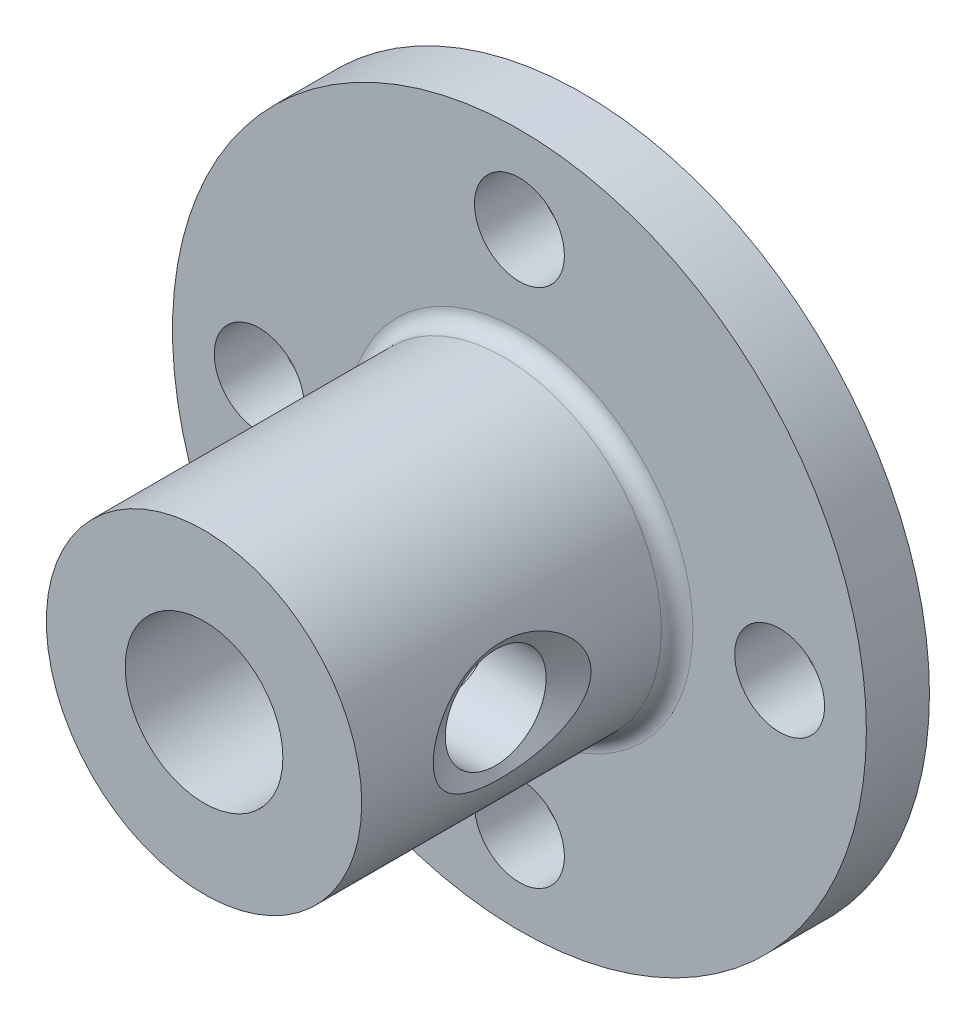
SolidWorks part; units mm, degrees
material "Cast Alloy Steel"
ref_plane "Front Plane" through (0, 0, 0) normal (0, 0, 1) x (1, 0, 0)
ref_plane "Top Plane" through (0, 0, 0) normal (0, 1, 0) x (1, 0, 0)
ref_plane "Right Plane" through (0, 0, 0) normal (1, 0, 0) x (0, 0, -1)
sketch "Sketch1" plane through (0, 0, 0) normal (0, 0, 1) x (1, 0, 0)
  circle A0 centre (0, 0) radius 2.5
  circle A1 centre (0, 0) radius 5
  circle A2 centre (0, 0) radius 11
sketch "Sketch3" plane through (0, 0, 0) normal (0, 0, 1) x (1, 0, 0)
  circle A0 centre (0, 0) radius 2.5
  circle A1 centre (0, 0) radius 5
  circle A2 centre (0, 0) radius 11
extrude "Boss-Extrude2" add sketch "Sketch1" along normal blind 12 contours A1 A0
extrude "Boss-Extrude3" add sketch "Sketch3" along normal blind 2 contours A2 A1
fillet "Fillet1" radius 0.5 1 edges at (5, 0, 2)
sketch "Sketch5" plane through (0, 0, 2) normal (0, 0, 1) x (1, 0, 0)
  line L0 (0, 0) -> (0, 11)
  line L1 (0, -6.6) -> (0, 6.6) construction
  line L2 (0, 11) -> (0, 5.5)
  line L3 (0, 5.5) -> (0, 8.25)
  line L4 (0, 0) -> (0, -11)
  line L5 (0, -11) -> (0, -5.5)
  circle A0 centre (0, 0) radius 11 construction
  circle A1 centre (0, 0) radius 8.25
  circle A2 centre (0, 8.25) radius 1.425
extrude "Cut-Extrude1" cut sketch "Sketch5" against normal blind 2 contours L2 A2 A1 | A1 A2 L2 | A1 A2 L3 | L3 A2 A1
pattern_circular "CirPattern1" count 4 over 360 about axis through (0, 0, 0) along (0, 0, 1) of "Cut-Extrude1"
hole_wizard "CSK for M3 Flat Head Machine Screw2" positions "3DSketch2" profile "Sketch8" countersink size "M3" standard "ANSI Metric" end condition through all
sketch3d "3DSketch2"
  point P0 (5, -0.0156, 7.2321)
sketch "Sketch8" plane through (5, -0.0156, 7.2321) normal (0, 0, 1) x (0.0031, 1, 0)
  line L0 (0, 0) -> (0, 16.0343)
  line L1 (0, 16.0343) -> (1.6, 16.0343)
  line L2 (1.6, 16.0343) -> (1.6, 0.5196)
  line L3 (1.6, 0.5196) -> (2.5, 0)
  line L5 (2.5, 0) -> (0, 0)
  line L6 (-1.6, 0.5196) -> (-2.5, 0) construction
  line L11 (0, -6.35) -> (0, 107.95) construction
  dimension "Thru Hole Dia." = 3.2
  dimension "Thru Hole Depth" = 16.0343
  dimension "Near C'Sink Dia." = 5
  dimension "Near C'Sink Angle" = 120
